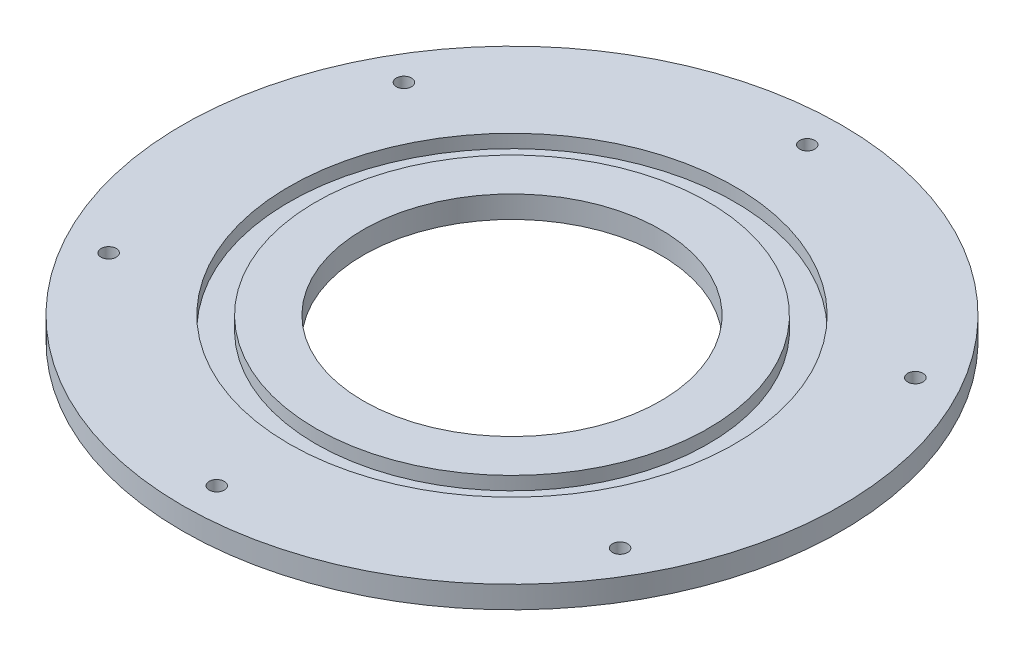
SolidWorks part; units mm, degrees
ref_plane "Front Plane" through (0, 0, 0) normal (0, 0, 1) x (1, 0, 0)
ref_plane "Top Plane" through (0, 0, 0) normal (0, 1, 0) x (1, 0, 0)
ref_plane "Right Plane" through (0, 0, 0) normal (1, 0, 0) x (0, 0, -1)
sketch "Sketch1" plane through (0, 0, 0) normal (0, 1, 0) x (1, 0, 0)
  circle A0 centre (0, 0) radius 86.5
  circle A1 centre (0, 0) radius 39
  dimension "D1" = 173
  dimension "D2" = 78
extrude "Boss-Extrude1" add sketch "Sketch1" along normal blind 5.8
sketch "Sketch2" plane through (0, 5.8, 0) normal (0, 1, 0) x (1, 0, 0)
  circle A0 centre (0, 0) radius 51.5
  circle A1 centre (0, 0) radius 58.5
  dimension "D1" = 103
  dimension "D2" = 117
extrude "Cut-Extrude1" cut sketch "Sketch2" against normal blind 3.5
sketch "Sketch3" plane through (0, 5.8, 0) normal (0, 1, 0) x (1, 0, 0)
  circle A0 centre (0, 0) radius 77.5 construction
  circle A1 centre (0, 77.5) radius 2
  circle A2 centre (67.117, 38.75) radius 2
  circle A3 centre (67.117, -38.75) radius 2
  circle A4 centre (0, -77.5) radius 2
  circle A5 centre (-67.117, -38.75) radius 2
  circle A6 centre (-67.117, 38.75) radius 2
  point P17 (0, 0)
  dimension "D1" = 155
  dimension "D2" = 4
  dimension "D3" = 6
extrude "Cut-Extrude2" cut sketch "Sketch3" against normal through all
